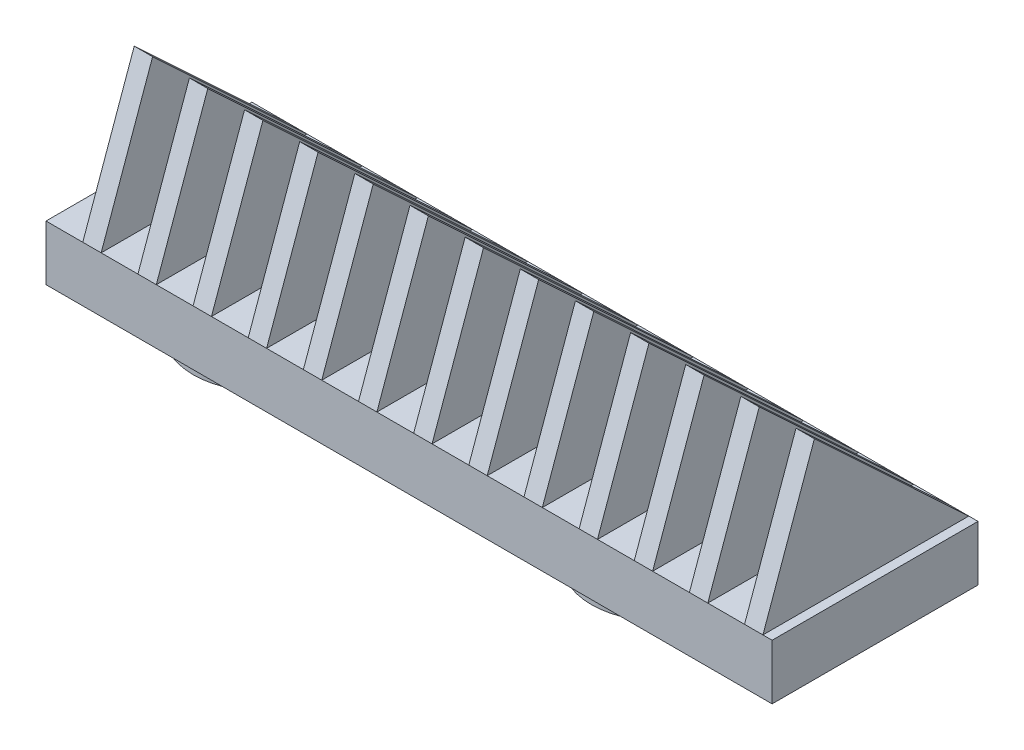
SolidWorks part; units mm, degrees
ref_plane "Front Plane" through (0, 0, 0) normal (0, 0, 1) x (1, 0, 0)
ref_plane "Top Plane" through (0, 0, 0) normal (0, 1, 0) x (1, 0, 0)
ref_plane "Right Plane" through (0, 0, 0) normal (1, 0, 0) x (0, 0, -1)
sketch "Sketch1" plane through (0, 0, 0) normal (0, 1, 0) x (1, 0, 0)
  line L1 (0, 0) -> (-211.1375, 0)
  line L2 (0, 0) -> (0, 35.56)
  line L3 (0, 35.56) -> (-211.1375, 35.56)
  line L4 (-211.1375, 0) -> (-211.1375, 35.56)
  dimension "D1" = 211.1375
extrude "Boss-Extrude1" add sketch "Sketch1" along normal blind 9.525
sketch "Sketch2" plane through (0, 9.525, 0) normal (0, 1, 0) x (1, 0, 0)
  line L0 (-211.1375, 0) -> (0, 0) construction
  line L1 (-211.1375, 35.56) -> (-207.8355, 35.56)
  line L2 (-211.1375, 35.56) -> (-211.1375, 0)
  line L3 (-211.1375, 0) -> (-207.8355, 0)
  line L4 (-207.8355, 35.56) -> (-207.8355, 0)
  dimension "D1" = 3.302
ref_plane "Plane1" through (0, 34.417, 0) normal (0, 1, 0) x (1, 0, 0)
sketch "Sketch5" plane through (0, 34.417, 0) normal (0, 1, 0) x (1, 0, 0)
  line L2 (-213.741, 8.89) -> (-207.8355, 8.89)
  line L3 (-207.8355, 35.56) -> (-207.8355, 0) construction
sketch "Sketch6" plane through (0, 0, 0) normal (0, -1, 0) x (-1, 0, 0)
  line L5 (0, 0) -> (0, 35.56) construction
  line L6 (211.1375, 35.56) -> (211.1375, 0) construction
  circle A0 centre (105.5687, 17.78) radius 12.192
  circle A1 centre (36.7982, 17.78) radius 12.192
  circle A2 centre (174.3392, 17.78) radius 12.192
  dimension "D1" = 36.7982
  dimension "D2" = 24.384
  dimension "D3" = 68.7705
  dimension "D4" = 24.384
  dimension "D5" = 24.384
  dimension "D6" = 36.7983
  dimension "D7" = 68.7705
extrude "Boss-Extrude4" add sketch "Sketch6" along normal blind 6.35
sketch3d "3DSketch1"
  line L0 (-207.8355, 9.525, -35.56) -> (-207.8355, 9.525, 0)
  line L1 (-207.8355, 9.525, 0) -> (-207.8355, 34.417, -8.89)
  line L2 (-207.8355, 34.417, -8.89) -> (-207.8355, 9.525, -35.56)
ref_plane "Plane2" through (-204.7875, 0, 0) normal (-1, 0, 0) x (0, 0, 1)
sketch "Sketch9" plane through (-204.7875, 0, 0) normal (-1, 0, 0) x (0, 0, 1)
  line L0 (-35.56, 9.525) -> (0, 9.525)
  line L1 (0, 9.525) -> (-8.89, 34.417)
  line L2 (-8.89, 34.417) -> (-35.56, 9.525)
extrude "Boss-Extrude5" add sketch "Sketch9" against normal blind 3.175
pattern_linear "LPattern1" count 22 spacing 9.525 along (1, 0, 0) of "Boss-Extrude5"
sketch "Sketch10" plane through (-211.1375, 0, 0) normal (-1, 0, 0) x (0, 0, 1)
  line L1 (-39.7052, -26.2761) -> (5.8449, -26.2761)
  line L2 (-39.7052, -26.2761) -> (-39.7052, 35.8171)
  line L3 (-39.7052, 35.8171) -> (5.8449, 35.8171)
  line L4 (5.8449, -26.2761) -> (5.8449, 35.8171)
  line L5 (-39.7052, -26.2761) -> (5.8449, 35.8171) construction
  line L6 (-39.7052, 35.8171) -> (5.8449, -26.2761) construction
  point P0 (-16.9302, 4.7705)
extrude "Cut-Extrude1" cut sketch "Sketch10" against normal up to surface (85.725 mm away) up to face at (-125.4125, 17.8223, -14.8167)
sketch "Sketch11" plane through (-125.4125, 0, 0) normal (-1, 0, 0) x (0, 0, 1)
  line L4 (-30.48, 0.9525) -> (-5.08, 0.9525)
  line L5 (-30.48, 0.9525) -> (-30.48, 8.5725)
  line L6 (-30.48, 8.5725) -> (-5.08, 8.5725)
  line L7 (-5.08, 0.9525) -> (-5.08, 8.5725)
  line L8 (-30.48, 0.9525) -> (-5.08, 8.5725) construction
  line L9 (-30.48, 8.5725) -> (-5.08, 0.9525) construction
  point P6 (-17.78, 4.7625)
  dimension "D1" = 25.4
  dimension "D2" = 7.62
extrude "Cut-Extrude2" cut sketch "Sketch11" against normal blind 12.7 contours L7 L6 L5 L4
